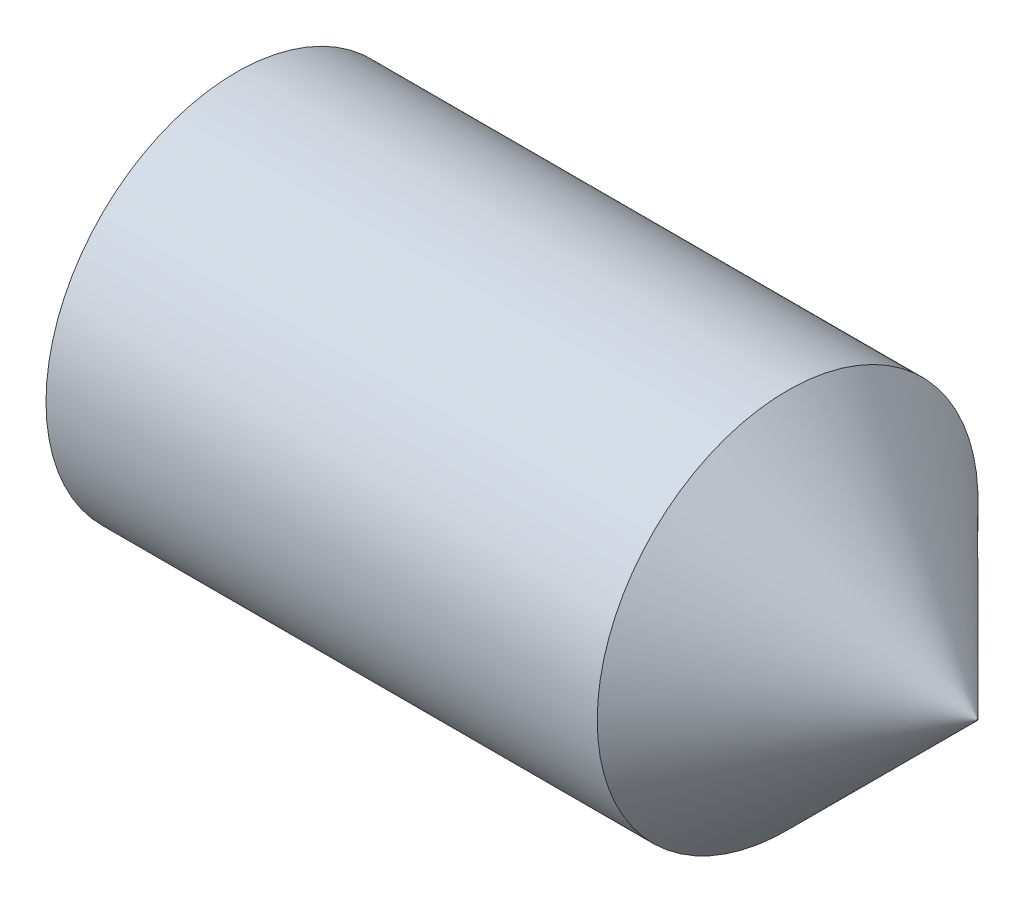
SolidWorks part; units mm, degrees
ref_plane "Plane1" through (0, 0, 0) normal (0, 0, 1) x (1, 0, 0)
ref_plane "Plane2" through (0, 0, 0) normal (0, 1, 0) x (1, 0, 0)
ref_plane "Plane3" through (0, 0, 0) normal (1, 0, 0) x (0, 0, -1)
sketch "BodySke" plane through (0, 0, 0) normal (0, 0, 1) x (1, 0, 0)
  line L0 (0, 0) -> (0, 1.2195)
  line L1 (0, 1.2195) -> (0.1619, 1.5)
  line L2 (0.1619, 1.5) -> (4.505, 1.5)
  line L3 (6, 0) -> (6, 0.005)
  line L4 (6, 0) -> (0, 0)
  line L5 (-12.7, 0) -> (88.9, 0) construction
  line L6 (6, 0.005) -> (4.505, 1.5)
  line L7 (0.5, 15.875) -> (0.5, -3.175) construction
  line L8 (0, -1.2195) -> (0.1619, -1.5) construction
  line L9 (6, -0.005) -> (4.505, -1.5) construction
  dimension "Cone_ang" = 90
  dimension "Length" = 6
  dimension "Diameter" = 3
  dimension "Drive_ch_ang" = 60
  dimension "Minor_dia" = 2.439
  dimension "Advance" = 0.5
  dimension "Tip_dia" = 0.01
revolve "BaseBody" add sketch "BodySke" angle 360 about L5
cosmetic thread "ThreadCosmetic" [suppressed] parameters "Thread_minor"=2.439
sketch "Sketch2" plane through (0, 0, 0) normal (-1, 0, 0) x (0, 0, 1)
  line L0 (0.433, 0.75) -> (-0.433, 0.75)
  line L1 (-0.433, 0.75) -> (-0.866, 0)
  line L2 (0.433, 0.75) -> (0.866, 0)
  line L3 (0.433, -0.75) -> (0.866, 0)
  line L4 (0.433, -0.75) -> (-0.433, -0.75)
  line L5 (-0.433, -0.75) -> (-0.866, 0)
  dimension "Hex_size" = 1.5
  dimension "D2" = 0.75
  dimension "D3" = 0.75
extrude "Hex" cut sketch "Sketch2" against normal blind 2.1
sketch "Sketch4" plane through (0, 4.7709, -0.5249) normal (-1, 0, 0) x (0, 0, 1)
  line L0 (0.5249, -4.7709) -> (1.3124, -4.7709)
  line L1 (0.5249, -4.7709) -> (6.6732, -1.2211) construction
  line L2 (0.5249, -4.7709) -> (0.9186, -4.0889)
  line L3 (1.153, -4.6137) -> (1.2782, -4.5415)
  line L4 (0.975, -4.3054) -> (1.1002, -4.2332)
  arc A0 (1.153, -4.6137) -> (0.975, -4.3054) centre (0.5249, -4.7709) ccw
  arc A1 (1.3124, -4.7709) -> (1.2782, -4.5415) centre (0.5249, -4.7709) ccw
  arc A2 (0.9186, -4.0889) -> (1.1002, -4.2332) centre (0.5249, -4.7709) cw
  circle A3 centre (0.5249, -4.7709) radius 0.6475 construction
  circle A4 centre (0.5249, -4.7709) radius 0.7875 construction
  dimension "D1" = 30
  dimension "Spline_n_dim" = 1.295
  dimension "Spline_m_dim" = 1.575
  dimension "Spline_a_dim" = 60
  dimension "D3" = 0.178
  dimension "Spline_p_dim" = 0.356
extrude "Spline6" [suppressed] cut sketch "Sketch4" against normal blind 1.2
pattern_circular "CirPattern1" [suppressed] count 6 every 60 about axis through (-12.7, 0, 0) along (1, 0, 0)
sketch "Sketch5" plane through (0, 1.4735, 6.925) normal (-1, 0, 0) x (0, 0, 1)
  line L0 (-6.925, -1.4735) -> (-6.1375, -1.4735)
  line L1 (-6.925, -1.4735) -> (-1.9049, 3.5466) construction
  line L2 (-6.925, -1.4735) -> (-6.925, -0.686)
  line L3 (-6.3413, -1.1415) -> (-6.2567, -1.0569)
  line L4 (-6.5931, -0.8898) -> (-6.5085, -0.8052)
  line L5 (-6.5931, -0.8898) -> (-6.3413, -1.1415)
  arc A1 (-6.1375, -1.4735) -> (-6.2567, -1.0569) centre (-6.925, -1.4735) ccw
  arc A2 (-6.925, -0.686) -> (-6.5085, -0.8052) centre (-6.925, -1.4735) cw
  circle A3 centre (-6.925, -1.4735) radius 0.6475 construction
  circle A4 centre (-6.925, -1.4735) radius 0.7875 construction
  dimension "D1" = 45
  dimension "Spline_n_dim" = 1.295
  dimension "Spline_m_dim" = 1.575
  dimension "Spline_a_dim" = 90
  dimension "D3" = 0.178
  dimension "Spline_p_dim" = 0.356
extrude "Spline4" [suppressed] cut sketch "Sketch5" against normal blind 1.2
pattern_circular "CirPattern2" [suppressed] count 4 every 90 about axis through (-12.7, 0, 0) along (1, 0, 0)
sketch "ThdSchSke" plane through (0, 0, 0) normal (0, 0, 1) x (1, 0, 0)
  line L0 (0.1619, -1.2195) -> (-0.0345, -1.5)
  line L1 (0.1619, -1.2195) -> (0.3584, -1.5)
  line L2 (0.3584, -1.5) -> (0.3584, -1.875)
  line L3 (-3.175, 0) -> (5.1513, 0) construction
  line L4 (0.1619, 1.5) -> (0.1619, -1.5) construction
  line L5 (0.3584, -1.875) -> (-0.0345, -1.875)
  line L6 (-0.0345, -1.875) -> (-0.0345, -1.5)
  dimension "Thread_minor" = 2.439
  dimension "Diameter" = 3
  dimension "SideAngle" = 55
  dimension "VeeAngle" = 70
  dimension "Overcut" = 3.75
revolve "ThreadSchematic" [suppressed] cut sketch "ThdSchSke" angle 360 about L3
pattern_linear "ThdSchPat" [suppressed]
equation "\"D2@Sketch2\" = \"Hex_size@Sketch2\" / 2"
equation "\"D3@Sketch2\" = \"Hex_size@Sketch2\" / 2"
equation "\"Thread_minor@ThreadCosmetic\" = \"Minor_dia@BodySke\""
equation "\"D1@Sketch4\" = \"Spline_a_dim@Sketch4\" / 2"
equation "\"D3@Sketch4\" = \"Spline_p_dim@Sketch4\" / 2"
equation "\"D2@CirPattern1\" = \"Spline_a_dim@Sketch4\""
equation "\"Num_teeth@CirPattern1\" = 360 / \"D2@CirPattern1\""
equation "\"Spline_a_dim@Sketch5\" = 90"
equation "\"Spline_p_dim@Sketch5\" = \"Spline_p_dim@Sketch4\""
equation "\"Spline_m_dim@Sketch5\" = \"Spline_m_dim@Sketch4\""
equation "\"Spline_n_dim@Sketch5\" = \"Spline_n_dim@Sketch4\""
equation "\"D1@Sketch5\" = \"Spline_a_dim@Sketch5\" / 2"
equation "\"D3@Sketch5\" = \"Spline_p_dim@Sketch5\" / 2"
equation "\"Key_eng@Spline4\" = \"Key_eng@Spline6\""
equation "\"Thread_minor@ThdSchSke\" = \"Thread_minor@ThreadCosmetic\""
equation "\"Diameter@ThdSchSke\" = \"Diameter@BodySke\""
equation "\"Overcut@ThdSchSke\" = \"Diameter@BodySke\" * 1.25"
equation "\"Num_threads@ThdSchPat\" = int( (\"Length@BodySke\" - ( ( ( \"Diameter@BodySke\" - \"Minor_dia@BodySke\" ) * 0.5 ) / tan( \"Drive_ch_ang@BodySke\" * 0.017453292 ) ) - ( ( \"Diameter@BodySke\" * 0.5 ) / tan( \"Cone_ang@BodySke\" * 0.008726646 ) ) ) / \"Advance@BodySke\" + 0.999 )  + 1"
equation "\"Num_threads@ThdSchPat\" = int( (\"Length@BodySke\" - ( ( ( \"Diameter@BodySke\" - \"Minor_dia@BodySke\" ) * 0.5 ) / tan( \"Drive_ch_ang@BodySke\" * 0.017453292 ) ) - ( (( \"Diameter@BodySke\" - \"Tip_dia@BodySke\") * 0.5 ) / tan( \"Cone_ang@BodySke\" * 0.008726646 ) ) ) / \"Advance@BodySke\" + 0.999 )  + 1"
equation "\"Advance@ThdSchPat\" = (\"Length@BodySke\" - ( ( ( \"Diameter@BodySke\" - \"Minor_dia@BodySke\" ) * 0.5 ) / tan( \"Drive_ch_ang@BodySke\" * 0.017453292 ) ) - ( ( \"Diameter@BodySke\" * 0.5 ) / tan( \"Cone_ang@BodySke\" * 0.008726646 ) ) ) /  (\"Num_threads@ThdSchPat\" - 1) 'relax it"
equation "\"Advance@ThdSchPat\" = (\"Length@BodySke\" - ( ( ( \"Diameter@BodySke\" - \"Minor_dia@BodySke\" ) * 0.5 ) / tan( \"Drive_ch_ang@BodySke\" * 0.017453292 ) ) - ( ( (\"Diameter@BodySke\" - \"Tip_dia@BodySke\") * 0.5 ) / tan( \"Cone_ang@BodySke\" * 0.008726646 ) ) ) /  (\"Num_threads@ThdSchPat\" - 1) 'relax it"
equation "' \"Num_threads@ThdSchPat\" = \"Num_threads@ThdSchPat\" - sgn( \"Num_threads@ThdSchPat\" - 1) '---chamfered tips only---"
